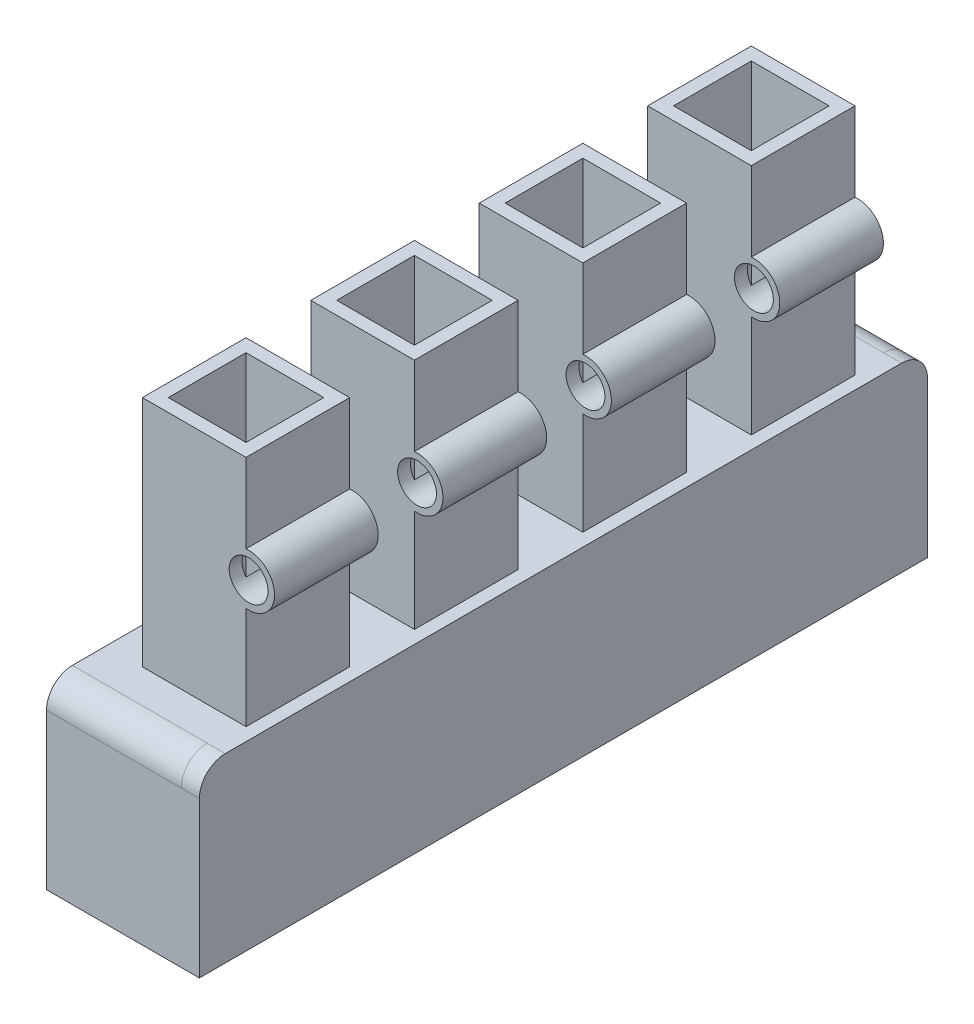
SolidWorks part; units mm, degrees
ref_plane "Front Plane" through (0, 0, 0) normal (0, 0, 1) x (1, 0, 0)
ref_plane "Top Plane" through (0, 0, 0) normal (0, 1, 0) x (1, 0, 0)
ref_plane "Right Plane" through (0, 0, 0) normal (1, 0, 0) x (0, 0, -1)
sketch "Sketch1" plane through (0, 0, 0) normal (1, 0, 0) x (0, 0, -1)
  line L14 (0, 30.0454) -> (0, 0) construction
  line L15 (-130.5, 0) -> (130.5, 0)
  line L16 (140.5, -10) -> (140.5, -70)
  line L17 (140.5, -70) -> (122.5, -70)
  line L18 (0, -70) -> (0, -67.0938)
  line L19 (7.5, -70) -> (-7.5, -70)
  line L20 (72.5, -70) -> (57.5, -70)
  line L21 (-72.5, -70) -> (-57.5, -70)
  line L22 (-140.5, -70) -> (-122.5, -70)
  line L23 (-140.5, -10) -> (-140.5, -70)
  arc A0 (130.5, 0) -> (140.5, -10) centre (130.5, -10) cw
  arc A1 (122.5, -70) -> (72.5, -70) centre (97.5, -70) ccw
  arc A2 (57.5, -70) -> (7.5, -70) centre (32.5, -70) ccw
  arc A3 (-57.5, -70) -> (-7.5, -70) centre (-32.5, -70) cw
  arc A4 (-122.5, -70) -> (-72.5, -70) centre (-97.5, -70) cw
  arc A5 (-130.5, 0) -> (-140.5, -10) centre (-130.5, -10) ccw
  dimension "D1" = 50
  dimension "D2" = 50
  dimension "D7" = 10
  dimension "D3" = 15
  dimension "D4" = 15
  dimension "D5" = 281
  dimension "D6" = 70
extrude "Boss-Extrude1" add sketch "Sketch1" along normal blind 50
sketch "Sketch2" plane through (0, 0, 0) normal (-1, 0, 0) x (0, 0, 1)
  line L1 (0, 0) -> (130.5, 0)
  line L12 (140.5, -10) -> (140.5, -70)
  line L13 (140.5, -70) -> (135.5, -70)
  line L14 (140.5, -70) -> (122.5, -70) construction
  line L15 (135.5, -70) -> (135.5, -15)
  line L16 (125.5, -5) -> (0, -5)
  line L17 (0, -5) -> (0, 0)
  arc A12 (130.5, 0) -> (140.5, -10) centre (130.5, -10) cw
  arc A13 (135.5, -15) -> (125.5, -5) centre (125.5, -15) ccw
  dimension "D3" = 10
  dimension "D1" = 5
  dimension "D2" = 5
extrude "Boss-Extrude2" add sketch "Sketch2" along normal blind 9
sketch "Sketch3" plane through (0, 0, 0) normal (-1, 0, 0) x (0, 0, 1)
  line L0 (0, 0) -> (0, -5)
  line L1 (0, -5) -> (-125.5, -5)
  line L2 (-135.5, -15) -> (-135.5, -70)
  line L3 (-140.5, -70) -> (-122.5, -70) construction
  line L4 (-135.5, -70) -> (-140.5, -70)
  line L5 (-140.5, -70) -> (-140.5, -10)
  line L6 (0, 0) -> (-130.5, 0) construction
  line L7 (-130.5, 0) -> (0, 0)
  arc A0 (-125.5, -5) -> (-135.5, -15) centre (-125.5, -15) ccw
  arc A1 (-140.5, -10) -> (-130.5, 0) centre (-130.5, -10) cw
  arc A2 (-130.5, 0) -> (-140.5, -10) centre (-130.5, -10) ccw construction
  dimension "D2" = 10
  dimension "D1" = 5
extrude "Boss-Extrude3" add sketch "Sketch3" along normal blind 9
sketch "Sketch5" plane through (0, 0, 0) normal (0, 1, 0) x (1, 0, 0)
  line L0 (50, -122.5) -> (50, -72.5) construction
  line L2 (50, -122.5) -> (0, -122.5) construction
  line L3 (50, -57.5) -> (50, -7.5) construction
  line L4 (50, -7.5) -> (0, -7.5) construction
  line L5 (50, 7.5) -> (0, 7.5) construction
  line L6 (50, 7.5) -> (50, 57.5) construction
  line L7 (50, 72.5) -> (0, 72.5) construction
  line L8 (50, 72.5) -> (50, 122.5) construction
  circle A0 centre (25, -97.5) radius 15
  circle A1 centre (25, -32.5) radius 15
  circle A2 centre (25, 32.5) radius 15
  circle A3 centre (25, 97.5) radius 15
  point P22 (25, 72.5)
  dimension "D1" = 30
  dimension "D2" = 30
  dimension "D3" = 30
  dimension "D4" = 30
  dimension "D5" = 25
  dimension "D6" = 25
  dimension "D7" = 25
  dimension "D8" = 25
  dimension "D9" = 25
  dimension "D10" = 25
  dimension "D11" = 25
  dimension "D12" = 25
sketch "Sketch6" plane through (0, 0, 0) normal (0, 1, 0) x (1, 0, 0)
  line L0 (50, -140.5) -> (50, 140.5)
  line L1 (50, 140.5) -> (43, 140.5)
  line L2 (50, 140.5) -> (-9, 140.5) construction
  line L3 (43, 140.5) -> (43, -140.5)
  line L4 (50, -140.5) -> (-9, -140.5) construction
  line L5 (43, -140.5) -> (50, -140.5)
  dimension "D1" = 7
extrude "Boss-Extrude4" add sketch "Sketch6" against normal blind 70
sketch "Sketch9" plane through (0, 0, 0) normal (0, 1, 0) x (1, 0, 0)
  line L0 (40, 47.5) -> (40, 17.5)
  line L1 (40, 112.5) -> (10, 112.5)
  line L2 (40, 112.5) -> (40, 82.5)
  line L3 (40, 82.5) -> (10, 82.5)
  line L4 (10, 112.5) -> (10, 82.5)
  line L9 (40, 47.5) -> (10, 47.5)
  line L10 (10, 47.5) -> (10, 17.5)
  line L11 (40, 17.5) -> (10, 17.5)
  line L12 (40, -17.5) -> (40, -47.5)
  line L13 (40, -17.5) -> (10, -17.5)
  line L14 (10, -17.5) -> (10, -47.5)
  line L15 (40, -47.5) -> (10, -47.5)
  line L16 (40, -82.5) -> (40, -112.5)
  line L17 (40, -82.5) -> (10, -82.5)
  line L18 (10, -82.5) -> (10, -112.5)
  line L19 (40, -112.5) -> (10, -112.5)
  dimension "D1" = 30
  dimension "D2" = 30
  dimension "D3" = 4
  dimension "D5" = 15
  dimension "D7" = 15
extrude "Cut-Extrude2" cut sketch "Sketch9" against normal through all both and the other way through all
sketch "Sketch10" plane through (0, 0, 0) normal (0, 1, 0) x (1, 0, 0)
  line L0 (10, 47.5) -> (10, 17.5)
  line L1 (10, 112.5) -> (40, 112.5)
  line L2 (10, 112.5) -> (10, 82.5)
  line L3 (10, 82.5) -> (40, 82.5)
  line L4 (40, 112.5) -> (40, 82.5)
  line L5 (5, 117.5) -> (45, 117.5)
  line L6 (5, 117.5) -> (5, 77.5)
  line L7 (5, 77.5) -> (45, 77.5)
  line L8 (45, 117.5) -> (45, 77.5)
  line L9 (10, 47.5) -> (40, 47.5)
  line L10 (40, 47.5) -> (40, 17.5)
  line L11 (10, 17.5) -> (40, 17.5)
  line L12 (5, 52.5) -> (5, 12.5)
  line L13 (5, 52.5) -> (45, 52.5)
  line L14 (45, 52.5) -> (45, 12.5)
  line L15 (5, 12.5) -> (45, 12.5)
  line L16 (10, -17.5) -> (10, -47.5)
  line L17 (10, -17.5) -> (40, -17.5)
  line L18 (40, -17.5) -> (40, -47.5)
  line L19 (10, -47.5) -> (40, -47.5)
  line L20 (5, -12.5) -> (5, -52.5)
  line L21 (5, -12.5) -> (45, -12.5)
  line L22 (45, -12.5) -> (45, -52.5)
  line L23 (5, -52.5) -> (45, -52.5)
  line L24 (10, -82.5) -> (10, -112.5)
  line L25 (10, -82.5) -> (40, -82.5)
  line L26 (40, -82.5) -> (40, -112.5)
  line L27 (10, -112.5) -> (40, -112.5)
  line L28 (5, -77.5) -> (5, -117.5)
  line L29 (5, -77.5) -> (45, -77.5)
  line L30 (45, -77.5) -> (45, -117.5)
  line L31 (5, -117.5) -> (45, -117.5)
  dimension "D1" = 40
  dimension "D2" = 40
  dimension "D3" = 5
  dimension "D4" = 5
  dimension "D5" = 4
extrude "Boss-Extrude7" add sketch "Sketch10" along normal blind 90
sketch "Sketch11" plane through (0, 0, 117.5) normal (0, 0, 1) x (1, 0, 0)
  line L0 (10, 90) -> (10, 0) construction
  line L1 (10, -50) -> (10, 90) construction
  line L2 (5, 90) -> (45, 90) construction
  line L3 (5, 0) -> (45, 0) construction
  line L4 (40, 90) -> (40, 0) construction
  line L5 (40, 50) -> (40, 45)
  line L6 (45, 79.0704) -> (45, 56.933) construction
  line L7 (45, 56.933) -> (45, 59.4499)
  line L8 (45, 39.5501) -> (45, 42.067)
  line L9 (45, 90) -> (45, 0) construction
  line L10 (45, 39.5501) -> (45, 42.067)
  line L11 (45, 42.067) -> (45, 33.9939) construction
  arc A0 (45, 42.067) -> (45, 56.933) centre (46, 49.5) ccw
  arc A1 (45, 39.5501) -> (45, 59.4499) centre (46, 49.5) ccw
  line M3 (45, 0) -> (45, 90)
  dimension "D3" = 15
  dimension "D4" = 20
  dimension "D1" = 5
  dimension "D2" = 45
  dimension "D5" = 6
extrude "Boss-Extrude8" add sketch "Sketch11" against normal blind 235 contours A1 A0 M3
sketch "Sketch12" plane through (0, 0, 0) normal (1, 0, 0) x (0, 0, -1)
  line L0 (-77.5, 90) -> (-77.5, 59.4499) construction
  line L1 (-77.5, 74.7249) -> (-52.5, 74.7249)
  line L2 (-77.5, 74.7249) -> (-77.5, 33.8217)
  line L3 (-77.5, 33.8217) -> (-52.5, 33.8217)
  line L4 (-52.5, 74.7249) -> (-52.5, 33.8217)
  line L5 (-52.5, 39.5501) -> (-52.5, 0) construction
  line L6 (-12.5, 90) -> (-12.5, 59.4499) construction
  line L7 (-12.5, 70.6705) -> (12.5, 70.6705)
  line L8 (-12.5, 70.6705) -> (-12.5, 31.932)
  line L9 (-12.5, 31.932) -> (12.5, 31.932)
  line L10 (12.5, 70.6705) -> (12.5, 31.932)
  line L11 (12.5, 39.5501) -> (12.5, 0) construction
  line L12 (52.5, 90) -> (52.5, 59.4499) construction
  line L13 (52.5, 67.1274) -> (77.5, 67.1274)
  line L14 (52.5, 67.1274) -> (52.5, 27.2078)
  line L15 (52.5, 27.2078) -> (77.5, 27.2078)
  line L16 (77.5, 67.1274) -> (77.5, 27.2078)
  line L17 (77.5, 39.5501) -> (77.5, 0) construction
extrude "Cut-Extrude3" cut sketch "Sketch12" along normal blind 235
sketch "Sketch13" plane through (0, 0, 117.5) normal (0, 0, 1) x (1, 0, 0)
  circle A0 centre (46, 49.5) radius 7.5
extrude "Cut-Extrude4" cut sketch "Sketch13" against normal blind 235
fillet "Fillet1" radius 10 2 edges at (46.5, 0, 140.5) (46.5, 0, -140.5)
